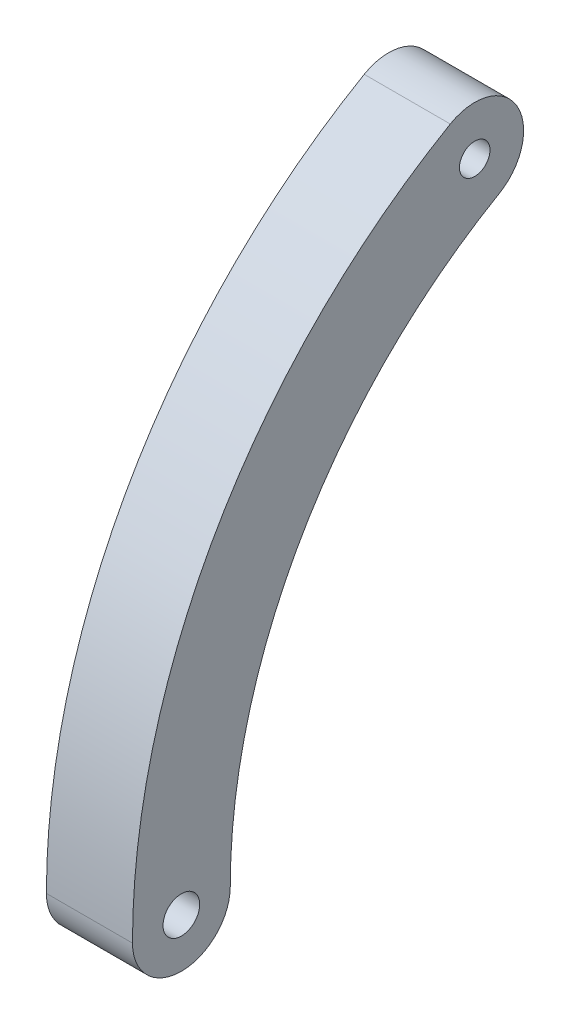
SolidWorks part; units mm, degrees
material "ABS"
ref_plane "Front Plane" through (0, 0, 0) normal (0, 0, 1) x (1, 0, 0)
ref_plane "Top Plane" through (0, 0, 0) normal (0, 1, 0) x (1, 0, 0)
ref_plane "Right Plane" through (0, 0, 0) normal (1, 0, 0) x (0, 0, -1)
sketch "Esquisse1" plane through (0, 0, 0) normal (1, 0, 0) x (0, 0, -1)
  arc A0 (-34.925, 0) -> (-17.4625, 30.2459) centre (0, 0) cw
  arc A1 (-41.275, 0) -> (-20.6375, 35.7452) centre (0, 0) cw
  arc A2 (-41.275, 0) -> (-34.925, 0) centre (-38.1, 0) ccw
  arc A3 (-17.4625, 30.2459) -> (-20.6375, 35.7452) centre (-19.05, 32.9956) ccw
  circle A4 centre (-38.1, 0) radius 1.1906
  circle A5 centre (-19.05, 32.9956) radius 0.9922
  dimension "D1" = 3.175
  dimension "D4" = 2.3812
  dimension "D5" = 1.9844
  dimension "D2" = 38.1
  dimension "D3" = 38.1
extrude "Boss.-Extru.1" add sketch "Esquisse1" along normal blind 5.588
